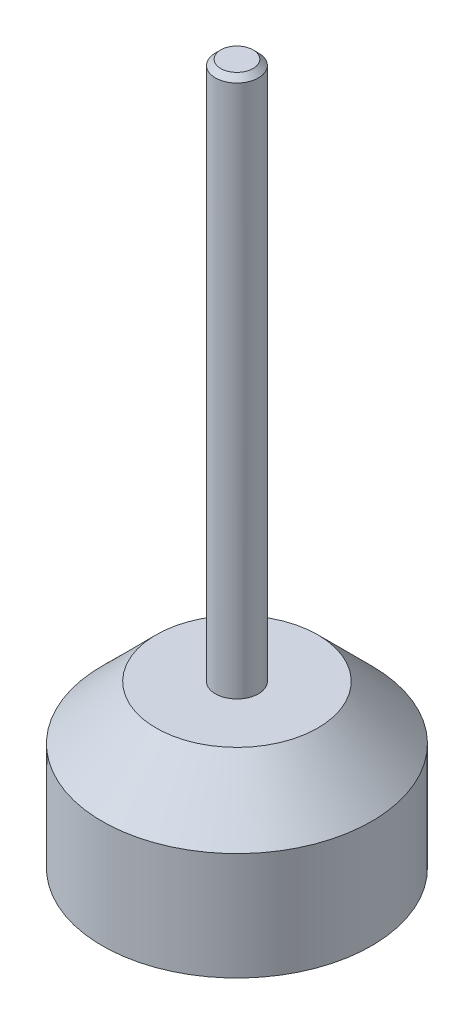
SolidWorks part; units mm, degrees
material "1.0402 (C22)"
ref_plane "Спереди" through (0, 0, 0) normal (0, 0, 1) x (1, 0, 0)
ref_plane "Сверху" through (0, 0, 0) normal (0, 1, 0) x (1, 0, 0)
ref_plane "Справа" through (0, 0, 0) normal (1, 0, 0) x (0, 0, -1)
sketch "Эскиз1" plane through (0, 0, 0) normal (0, 0, 1) x (1, 0, 0)
  line L0 (0, 0) -> (0, 94.7815) construction
  line L1 (0, 0) -> (25, 0)
  line L2 (25, 0) -> (25, 20)
  line L3 (25, 20) -> (15, 30)
  line L4 (15, 30) -> (4, 30)
  line L5 (4, 30) -> (4, 130)
  line L6 (4, 130) -> (0, 130)
  line L7 (0, 130) -> (0, 0)
  point P3 (0, 0)
  point P10 (25.0773, 30)
  point P11 (14.6022, 30)
  dimension "D1" = 30
  dimension "D2" = 20
  dimension "D3" = 8
  dimension "D4" = 50
  dimension "D5" = 30
  dimension "D6" = 130
revolve "Повернуть1" add sketch "Эскиз1" angle 360 about L0
chamfer "Фаска1" distance 1 angle 45 1 edges at (0, 130, -4)
